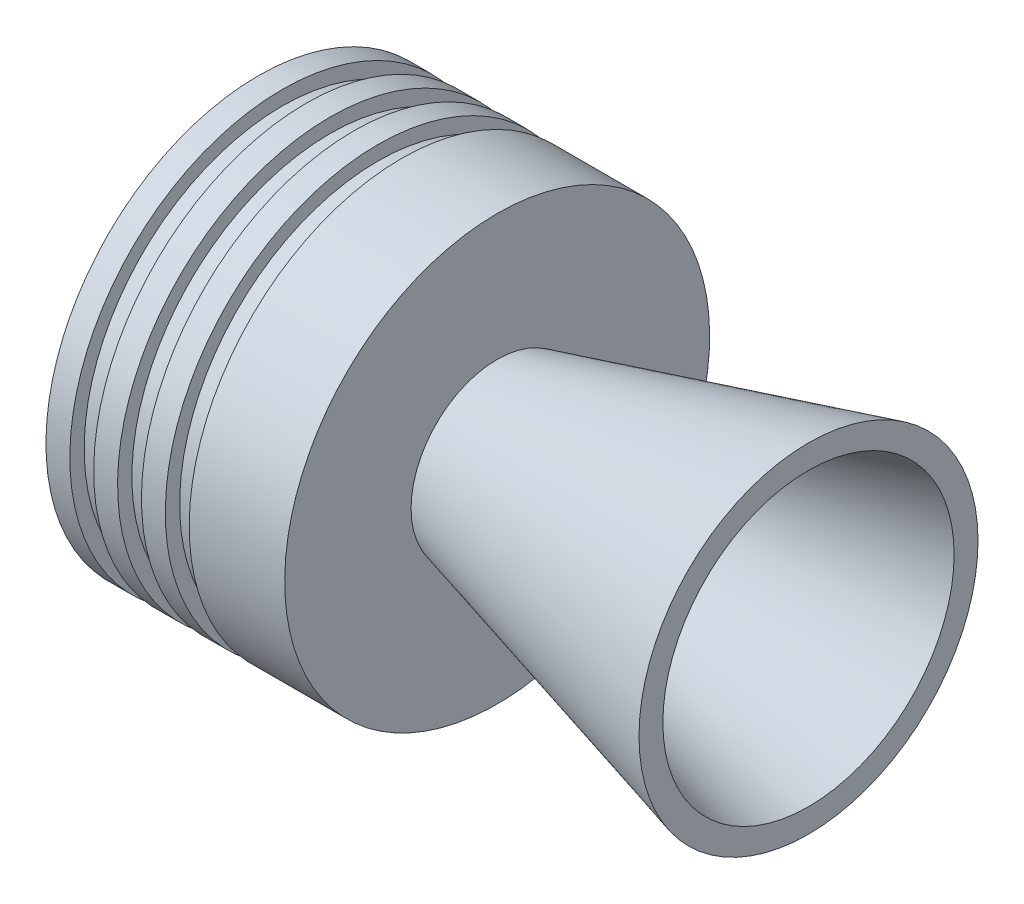
SolidWorks part; units mm, degrees
material "AISI 4130 Steel, annealed at 865C"
ref_plane "Front Plane" through (0, 0, 0) normal (0, 0, 1) x (1, 0, 0)
ref_plane "Top Plane" through (0, 0, 0) normal (0, 1, 0) x (1, 0, 0)
ref_plane "Right Plane" through (0, 0, 0) normal (1, 0, 0) x (0, 0, -1)
sketch "Sketch1" plane through (0, 0, 0) normal (0, 0, 1) x (1, 0, 0)
  line L0 (0, 0) -> (-126.4, 0) construction
  line L1 (-82.1051, 11.5) -> (0, 33.5)
  line L2 (-82.1051, 11.5) -> (-83.1051, 11.5)
  line L3 (-83.1051, 11.5) -> (-126.4, 36.4963)
  line L4 (-126.4, 36.4963) -> (-126.4, 44.4963)
  line L5 (-126.4, 44.4963) -> (-121.4, 44.4963)
  line L6 (-121.4, 44.4963) -> (-121.4, 41.4963)
  line L7 (-121.4, 41.4963) -> (-116.4, 41.4963)
  line L8 (-116.4, 41.4963) -> (-116.4, 44.4963)
  line L9 (-116.4, 44.4963) -> (-111.4, 44.4963)
  line L10 (-111.4, 44.4963) -> (-111.4, 41.4963)
  line L11 (-111.4, 41.4963) -> (-106.4, 41.4963)
  line L12 (-106.4, 41.4963) -> (-106.4, 44.4963)
  line L13 (-106.4, 44.4963) -> (-101.4, 44.4963)
  line L14 (-101.4, 44.4963) -> (-101.4, 41.4963)
  line L15 (-101.4, 41.4963) -> (-96.4, 41.4963)
  line L16 (-96.4, 41.4963) -> (-96.4, 44.4963)
  line L17 (-96.4, 44.4963) -> (-76.4, 44.4963)
  line L18 (-76.4, 44.4963) -> (-76.4, 18.0287)
  line L20 (0, 38.5) -> (0, 33.5)
  line L21 (-76.4, 18.0287) -> (0, 38.5)
  dimension "D1" = 126.4
  dimension "D2" = 11.5
  dimension "D3" = 15
  dimension "D4" = 33.5
  dimension "D5" = 1
  dimension "D6" = 30
  dimension "D7" = 8
  dimension "D8" = 5
  dimension "D9" = 3
  dimension "D10" = 5
  dimension "D11" = 5
  dimension "D12" = 5
  dimension "D13" = 5
  dimension "D14" = 5
  dimension "D15" = 26.4676
  dimension "D16" = 5
revolve "Revolve1" add sketch "Sketch1" angle 360 about L0
sketch "Sketch2" plane through (0, 0, 0) normal (0, 0, 1) x (1, 0, 0)
  line L0 (0, 0) -> (-76.4, 0) construction
  line L1 (-76.4, -44.4963) -> (-76.4, 44.4963) construction
  line L2 (-11.1962, 0) -> (-11.1962, 35.5)
  line L3 (0, 38.5) -> (-76.4, 18.0287) construction
  line L4 (-11.1962, 35.5) -> (-11.1962, 56.2719)
  line L5 (-11.1962, 56.2719) -> (14.5313, 56.2719)
  line L6 (14.5313, 56.2719) -> (14.5313, 0)
  line L7 (14.5313, 0) -> (-11.1962, 0)
  dimension "D1" = 35.5
revolve "Cut-Revolve1" cut sketch "Sketch2" angle 360 about L0
